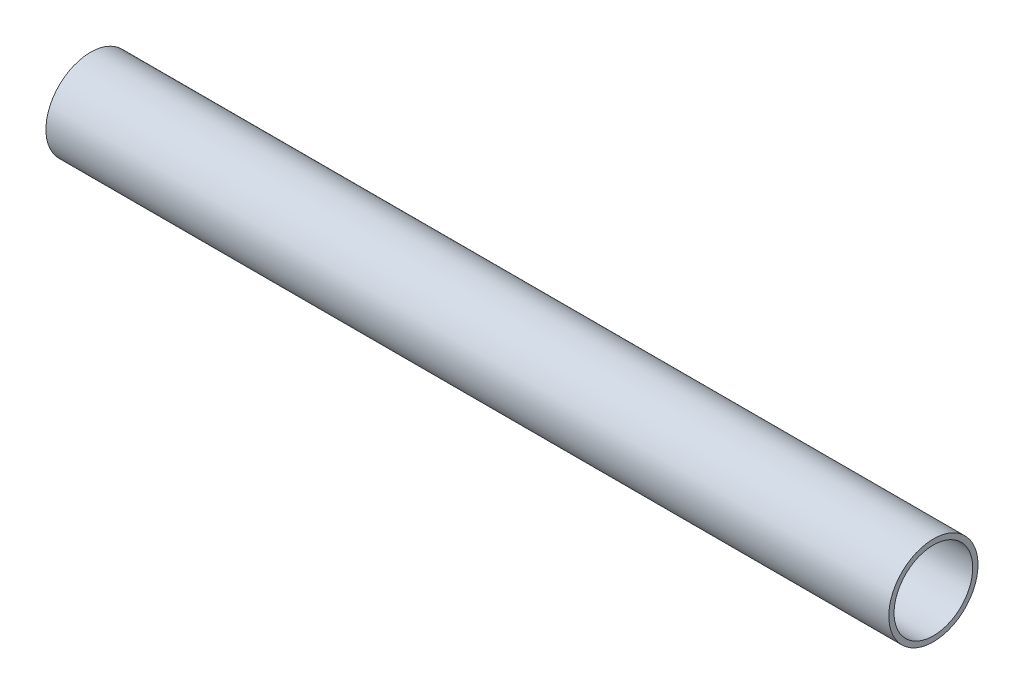
SolidWorks part; units mm, degrees
ref_plane "Plan de face" through (0, 0, 0) normal (0, 0, 1) x (1, 0, 0)
ref_plane "Plan de dessus" through (0, 0, 0) normal (0, 1, 0) x (1, 0, 0)
ref_plane "Plan de droite" through (0, 0, 0) normal (1, 0, 0) x (0, 0, -1)
sketch "Esquisse1" plane through (0, 0, 0) normal (1, 0, 0) x (0, 0, -1)
  circle A0 centre (0, 0) radius 1.5875
  circle A2 centre (0, 0) radius 1.4
  dimension "D1" = 3.175
  dimension "D2" = 2.8
extrude "Boss.-Extru.1" add sketch "Esquisse1" along normal blind 30
